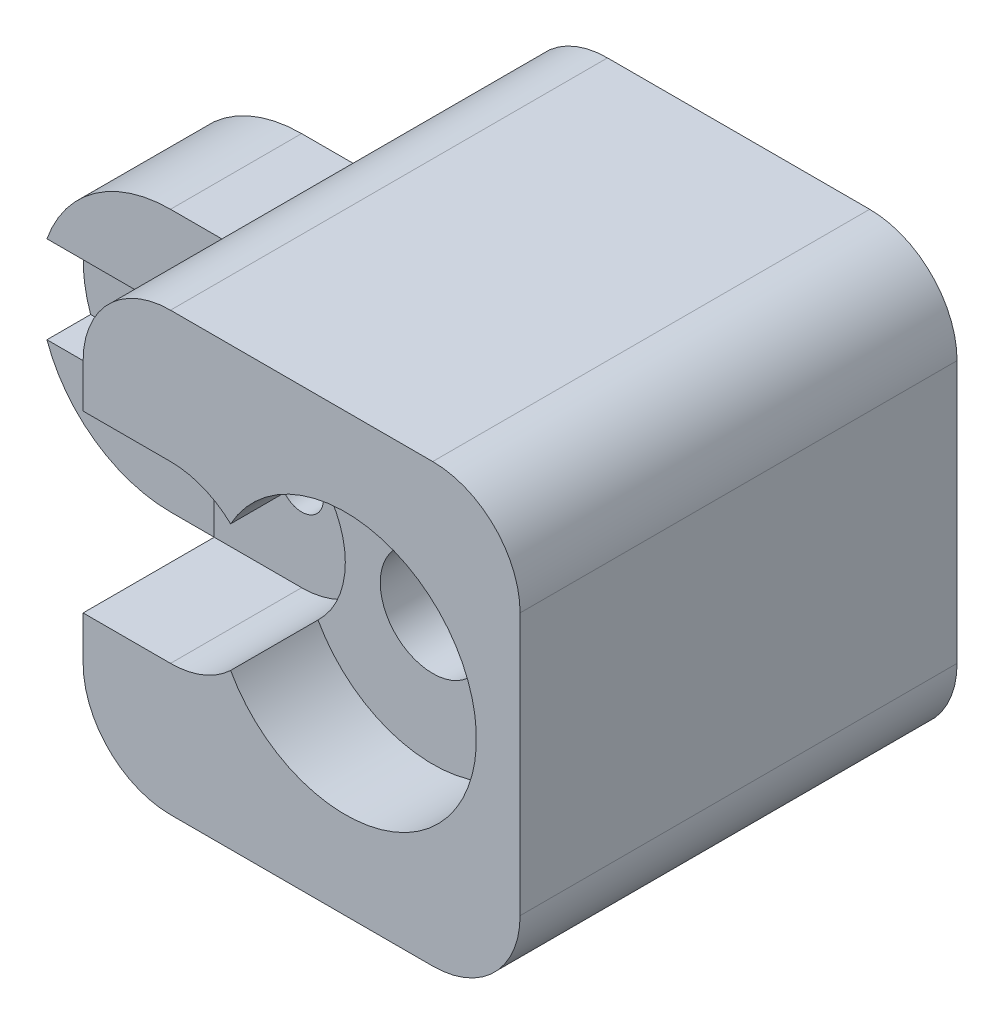
SolidWorks part; units mm, degrees
ref_plane "Front Plane" through (0, 0, 0) normal (0, 0, 1) x (1, 0, 0)
ref_plane "Top Plane" through (0, 0, 0) normal (0, 1, 0) x (1, 0, 0)
ref_plane "Right Plane" through (0, 0, 0) normal (1, 0, 0) x (0, 0, -1)
sketch "Sketch1" plane through (0, 0, 0) normal (0, 0, 1) x (1, 0, 0)
  line L1 (0, 0) -> (100, 0)
  line L2 (0, 0) -> (0, 100)
  line L3 (0, 100) -> (100, 100)
  line L4 (100, 0) -> (100, 100)
  dimension "D1" = 100
  dimension "D2" = 100
extrude "Boss-Extrude1" add sketch "Sketch1" along normal blind 100
sketch "Sketch2" plane through (0, 0, 100) normal (0, 0, 1) x (1, 0, 0)
  line L0 (100, 100) -> (0, 100) construction
  line L1 (0, 0) -> (100, 0) construction
  line L2 (0, 100) -> (0, 0) construction
  line L3 (0, 80) -> (0, 100)
  line L4 (0, 100) -> (20, 100)
  line L5 (80, 100) -> (100, 100)
  line L6 (100, 100) -> (100, 80)
  line L7 (80, 0) -> (100, 0)
  line L8 (100, 0) -> (100, 20)
  line L9 (0, 20) -> (0, 0)
  line L10 (0, 0) -> (20, 0)
  arc A0 (20, 100) -> (0, 80) centre (20, 80) ccw
  arc A1 (80, 100) -> (100, 80) centre (80, 80) cw
  arc A2 (80, 0) -> (100, 20) centre (80, 20) ccw
  arc A3 (0, 20) -> (20, 0) centre (20, 20) ccw
  dimension "D1" = 20
  dimension "D6" = 20
  dimension "D7" = 20
  dimension "D8" = 20
  dimension "D2" = 0
  dimension "D3" = 20
  dimension "D4" = 20
  dimension "D5" = 20
  dimension "D9" = 20
  dimension "D10" = 20
  dimension "D11" = 20
  dimension "D12" = 20
  dimension "D13" = 20
  dimension "D14" = 20
  dimension "D15" = 0
  dimension "D16" = 20
  dimension "D17" = 20
extrude "Cut-Extrude1" cut sketch "Sketch2" against normal blind 100
sketch "Sketch3" plane through (0, 0, 0) normal (0, 0, -1) x (-1, 0, 0)
  circle A0 centre (-60, 50) radius 12
  dimension "D1" = 24
  dimension "D2" = 40
  dimension "D3" = 50
extrude "Cut-Extrude2" cut sketch "Sketch3" against normal blind 80
ref_plane "Plane1" through (0, 0, 20) normal (0, 0, 1) x (1, 0, 0)
sketch "Sketch5" plane through (0, 0, 20) normal (0, 0, 1) x (1, 0, 0)
  circle A0 centre (20, 50) radius 5
  dimension "D1" = 10
  dimension "D2" = 20
  dimension "D3" = 50
extrude "Cut-Extrude3" cut sketch "Sketch5" along normal blind 50
ref_plane "Plane2" through (0, 0, 30) normal (0, 0, 1) x (1, 0, 0)
sketch "Sketch7" plane through (0, 0, 30) normal (0, 0, 1) x (1, 0, 0)
  line L0 (0, 80) -> (-20, 80)
  line L1 (0, 20) -> (-20, 20)
  line L2 (0, 80) -> (0, 20)
  arc A0 (-20, 80) -> (-20, 20) centre (-20, 50) ccw
  point P4 (0, 80)
  dimension "D5" = 30
  dimension "D1" = 20
  dimension "D2" = 20
  dimension "D3" = 0
  dimension "D4" = 0
extrude "Boss-Extrude2" add sketch "Sketch7" along normal blind 30
sketch "Sketch8" plane through (0, 0, 60) normal (0, 0, 1) x (1, 0, 0)
  circle A0 centre (-20, 50) radius 10
  dimension "D1" = 20
extrude "Cut-Extrude4" cut sketch "Sketch8" against normal blind 30
sketch "Sketch9" plane through (0, 0, 60) normal (0, 0, 1) x (1, 0, 0)
  line L0 (-20, 60) -> (-48.2843, 60)
  line L1 (-20, 40) -> (-48.2843, 40)
  circle A0 centre (-20, 50) radius 10 construction
  arc A1 (-20, 80) -> (-20, 20) centre (-20, 50) ccw construction
  arc A2 (-48.2843, 60) -> (-48.2843, 40) centre (-20, 50) ccw
  arc A3 (-20, 60) -> (-20, 40) centre (-20, 50) ccw
extrude "Cut-Extrude5" cut sketch "Sketch9" against normal blind 10
ref_plane "Plane3" through (0, 0, 30) normal (0, 0, 1) x (1, 0, 0)
sketch "Sketch10" plane through (0, 0, 30) normal (0, 0, 1) x (1, 0, 0)
  circle A0 centre (60, 50) radius 30
  dimension "D1" = 60
extrude "Cut-Extrude6" cut sketch "Sketch10" along normal blind 96
sketch "Sketch11" plane through (0, 0, 100) normal (0, 0, 1) x (1, 0, 0)
  line L0 (20, 70) -> (0, 70)
  line L1 (0, 80) -> (0, 20) construction
  line L2 (0, 70) -> (0, 30)
  line L3 (0, 30) -> (20, 30)
  arc A0 (20, 70) -> (20, 30) centre (20, 50) cw
  dimension "D1" = 20
  dimension "D2" = 20
extrude "Cut-Extrude7" cut sketch "Sketch11" against normal blind 30
sketch "Sketch14" plane through (0, 0, 70) normal (0, 0, 1) x (1, 0, 0)
  line L0 (20, 55) -> (20, 70)
  line L1 (20, 45) -> (20, 30)
  arc A0 (20, 70) -> (20, 30) centre (20, 50) cw
  circle A1 centre (20, 50) radius 5 construction
  arc A2 (20, 55) -> (20, 45) centre (20, 50) cw
  dimension "D1" = 15
extrude "Boss-Extrude5" add sketch "Sketch14" along normal blind 10
sketch "Sketch15" plane through (0, 0, 30) normal (0, 0, 1) x (1, 0, 0)
  circle A0 centre (60, 50) radius 30
  circle A1 centre (60, 50) radius 12
  dimension "D1" = 24
  dimension "D2" = 60
extrude "Boss-Extrude6" add sketch "Sketch15" along normal blind 40
sketch "Sketch16" plane through (0, 0, 70) normal (0, 0, 1) x (1, 0, 0)
  circle A0 centre (60, 50) radius 12
  arc A1 (33.75, 64.5237) -> (33.75, 35.4763) centre (60, 50) cw
  arc A2 (33.75, 35.4763) -> (33.75, 64.5237) centre (20, 50) ccw construction
  arc A3 (33.75, 64.5237) -> (33.75, 35.4763) centre (20, 50) cw
  circle M1 centre (60, 50) radius 12
  arc M2 (33.75, 64.5237) -> (33.75, 35.4763) centre (20, 50) cw
  arc M3 (33.75, 35.4763) -> (33.75, 64.5237) centre (60, 50) ccw
  dimension "D1" = 24
extrude "Boss-Extrude7" add sketch "Sketch16" along normal blind 10 contours M3 M2 M1
sketch "Sketch17" plane through (0, 0, 80) normal (0, 0, 1) x (1, 0, 0)
  line L0 (20, 70) -> (20, 55) construction
  line L1 (20, 45) -> (20, 30) construction
  line L2 (20, 55) -> (20, 70)
  line L3 (20, 45) -> (20, 30)
  arc A0 (20, 70) -> (20, 30) centre (20, 50) cw
  arc A1 (20, 30) -> (33.75, 35.4763) centre (20, 50) ccw construction
  arc A2 (20, 55) -> (20, 45) centre (20, 50) cw
  arc M1 (20, 30) -> (33.75, 35.4763) centre (20, 50) ccw
  arc M3 (33.75, 64.5237) -> (20, 70) centre (20, 50) ccw
  line M4 (20, 70) -> (20, 55)
  arc M5 (20, 55) -> (20, 45) centre (20, 50) cw
  line M6 (20, 45) -> (20, 30)
  dimension "D1" = 15
extrude "Cut-Extrude8" cut sketch "Sketch17" against normal blind 10 contours A0 M3 M4 M5 M6 M1
sketch "Sketch18" plane through (0, 0, 0) normal (0, 0, -1) x (-1, 0, 0)
  line L0 (-20, 70) -> (0, 70)
  line L1 (0, 80) -> (0, 20) construction
  line L2 (-20, 30) -> (0, 30)
  line L3 (0, 30) -> (0, 70)
  line L4 (0, 70) -> (0, 30)
  arc A0 (-20, 70) -> (-20, 30) centre (-20, 50) ccw
  line M3 (0, 20) -> (0, 80)
  dimension "D1" = 20
extrude "Cut-Extrude9" cut sketch "Sketch18" against normal blind 20 contours L0 A0 L2 M3
